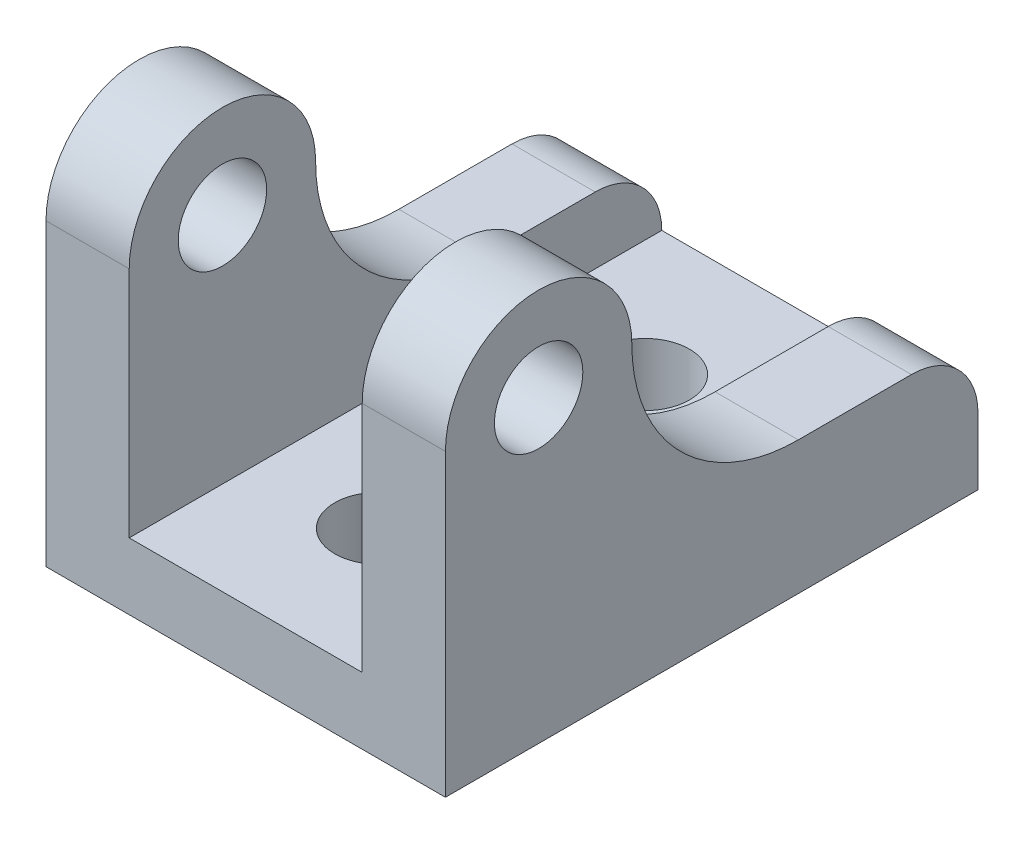
SolidWorks part; units mm, degrees
material "6061-T6 (SS)"
ref_plane "Front Plane" through (0, 0, 0) normal (0, 0, 1) x (1, 0, 0)
ref_plane "Top Plane" through (0, 0, 0) normal (0, 1, 0) x (1, 0, 0)
ref_plane "Right Plane" through (0, 0, 0) normal (1, 0, 0) x (0, 0, -1)
sketch "Sketch1" plane through (0, 0, 0) normal (0, 0, 1) x (1, 0, 0)
  line L0 (-19.05, 0) -> (19.05, 0)
  line L1 (19.05, 0) -> (19.05, 50.8)
  line L2 (19.05, 50.8) -> (11.1125, 50.8)
  line L3 (11.1125, 50.8) -> (11.1125, 6.35)
  line L4 (11.1125, 6.35) -> (-11.1125, 6.35)
  line L5 (0, 6.35) -> (0, 0) construction
  line L6 (-11.1125, 50.8) -> (-11.1125, 6.35)
  line L7 (-19.05, 50.8) -> (-11.1125, 50.8)
  line L8 (-19.05, 0) -> (-19.05, 50.8)
  point P4 (0, 0)
  dimension "D1" = 6.35
  dimension "D2" = 50.8
  dimension "D3" = 38.1
  dimension "D4" = 22.225
extrude "Boss-Extrude1" add sketch "Sketch1" along normal blind 50.8
sketch "Sketch5" plane through (0, 0, 0) normal (0, 1, 0) x (1, 0, 0)
  line L0 (0, 0) -> (0, -50.8) construction
  line L5 (-19.05, 0) -> (19.05, 0) construction
  line L6 (-19.05, -50.8) -> (19.05, -50.8) construction
  line L7 (-19.05, -25.4) -> (-19.05, 0) construction
  line L8 (19.05, -25.4) -> (-19.05, -25.4) construction
  line L9 (19.05, -50.8) -> (19.05, 0) construction
  line L10 (-19.05, -50.8) -> (-19.05, 0) construction
  line L11 (11.1125, -50.8) -> (11.1125, 0) construction
  line L12 (19.05, 0) -> (11.1125, 0) construction
  line L13 (19.05, 0) -> (19.05, -7.9375) construction
  line L14 (19.05, -7.9375) -> (11.1125, -7.9375) construction
  line L15 (11.1125, 0) -> (11.1125, -7.9375) construction
  line L16 (19.05, -7.9375) -> (11.1125, 0) construction
  line L17 (19.05, 0) -> (11.1125, -7.9375) construction
  line L18 (0, -12.7) -> (0, -38.1) construction
  point P8 (0, -25.4)
  point P19 (15.0813, -3.9688)
  point P24 (-15.0813, -3.9688)
  point P26 (-15.0812, -46.8312)
  point P27 (15.0813, -46.8312)
  point P29 (-19.05, -12.7)
hole_wizard "5/16 Clearance Hole3" positions "Sketch16" profile "Sketch17" hole size "5/16" standard "ANSI Inch" end condition through all
sketch "Sketch16" plane through (0, 6.35, 0) normal (0, 1, 0) x (1, 0, 0)
  point P0 (0, -38.1)
  point P3 (0, -12.7)
sketch "Sketch17" plane through (0, 6.35, 38.1) normal (1, 0, 0) x (0, 0, 1)
  line L0 (0, 0) -> (0, 6.35)
  line L1 (0, 6.35) -> (4.2164, 6.35)
  line L2 (4.2164, 6.35) -> (4.2164, 0)
  line L5 (4.2164, 0) -> (0, 0)
  line L11 (0, -6.35) -> (0, 107.95) construction
  dimension "Thru Hole Dia." = 8.4328
  dimension "Thru Hole Depth" = 6.35
sketch "Sketch18" plane through (0, 0, 0) normal (1, 0, 0) x (0, 0, -1)
  line L0 (-33.8836, 6.35) -> (-42.3164, 6.35) construction
  line L1 (-50.8, 50.8) -> (0, 50.8)
  line L2 (-50.8, 50.8) -> (-50.8, 6.35)
  line L3 (-50.8, 6.35) -> (0, 6.35)
  line L4 (0, 50.8) -> (0, 6.35)
  line L5 (0, 50.8) -> (0, 6.35) construction
  line L6 (-17.145, 12.7) -> (-6.35, 12.7)
  line L7 (-50.8, 28.575) -> (-50.8, 6.35)
  circle A0 centre (-41.91, 28.575) radius 3.9687 construction
  arc A1 (-50.8, 28.575) -> (-33.02, 28.575) centre (-41.91, 28.575) cw
  arc A2 (-33.02, 28.575) -> (-17.145, 12.7) centre (-17.145, 28.575) ccw
  arc A3 (-6.35, 12.7) -> (0, 6.35) centre (-6.35, 6.35) cw
  point P9 (-50.8, 28.575)
  point P10 (-41.91, 28.575)
  dimension "D2" = 7.9375
  dimension "D1" = 8.89
  dimension "D3" = 6.35
extrude "Cut-Extrude2" cut sketch "Sketch18" against normal through all both and the other way through all contours L6 A3 L4 L1 L2 A1 A2
hole_wizard "5/16 Clearance Hole2" positions "Sketch19" profile "Sketch20" hole size "5/16" standard "ANSI Inch" end condition through all
sketch "Sketch19" plane through (19.05, 0, 0) normal (1, 0, 0) x (0, 0, -1)
  point P0 (-41.91, 28.575)
sketch "Sketch20" plane through (19.05, 28.575, 41.91) normal (0, 1, 0) x (0, 0, -1)
  line L0 (0, 0) -> (0, 38.1)
  line L1 (0, 38.1) -> (4.2164, 38.1)
  line L2 (4.2164, 38.1) -> (4.2164, 0)
  line L5 (4.2164, 0) -> (0, 0)
  line L11 (0, -6.35) -> (0, 107.95) construction
  dimension "Thru Hole Dia." = 8.4328
  dimension "Thru Hole Depth" = 38.1
